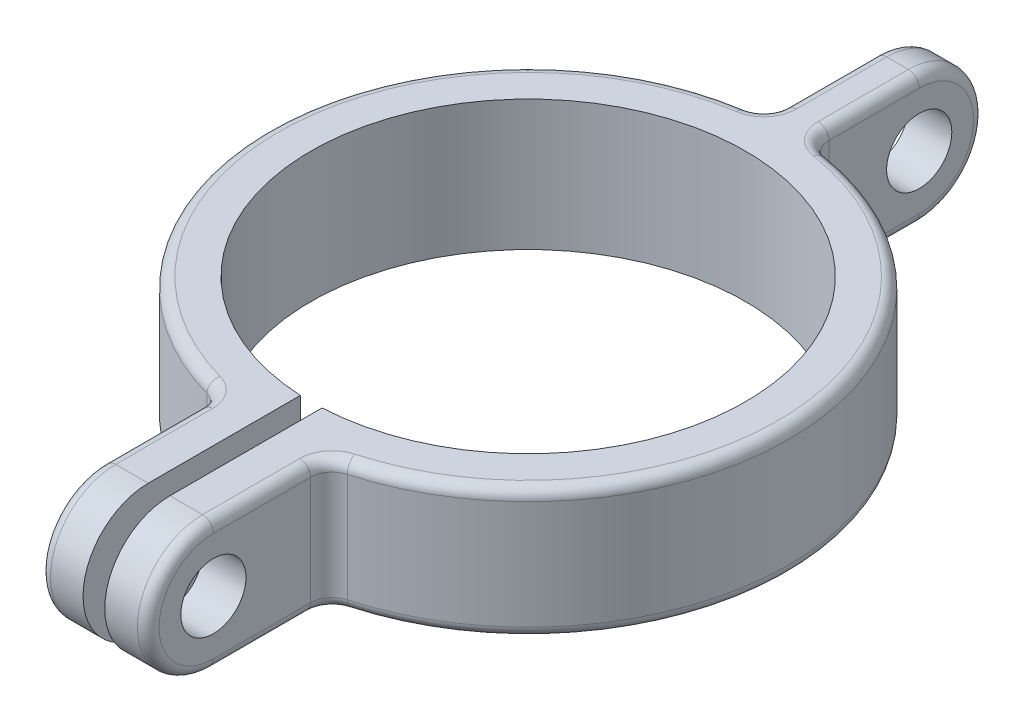
SolidWorks part; units mm, degrees
ref_plane "Front" through (0, 0, 0) normal (0, 0, 1) x (1, 0, 0)
ref_plane "Top" through (0, 0, 0) normal (0, 1, 0) x (1, 0, 0)
ref_plane "Right" through (0, 0, 0) normal (1, 0, 0) x (0, 0, -1)
sketch "Sketch1" plane through (0, 0, 0) normal (0, 1, 0) x (1, 0, 0)
  circle A0 centre (0, 0) radius 38.1
  circle A1 centre (0, 0) radius 31.75
  dimension "D1" = 63.5
  dimension "D2" = 76.2
extrude "Extrude1" add sketch "Sketch1" along normal blind 19.05
sketch "Sketch2" plane through (0, 19.05, 0) normal (0, 1, 0) x (-1, 0, 0)
  line L1 (-1.5875, 0) -> (1.5875, 0)
  line L2 (-1.5875, 0) -> (-1.5875, 40.64)
  line L3 (-1.5875, 40.64) -> (1.5875, 40.64)
  line L4 (1.5875, 0) -> (1.5875, 40.64)
  circle A0 centre (0, 0) radius 38.1 construction
  dimension "D2" = 2.54
  dimension "D1" = 3.175
extrude "Cut-Extrude1" cut sketch "Sketch2" against normal through all
sketch "Sketch3" plane through (1.5875, 0, 0) normal (-1, 0, 0) x (0, 0, 1)
  line L0 (31.7103, 19.05) -> (53.9419, 19.05)
  line L1 (53.9419, 0) -> (31.7103, 0)
  line L2 (31.7103, 19.05) -> (31.7103, 0)
  line L3 (38.0669, 0) -> (38.0669, 19.05) construction
  arc A0 (53.9419, 19.05) -> (53.9419, 0) centre (53.9419, 9.525) cw
  dimension "D1" = 15.875
extrude "Extrude2" add sketch "Sketch3" against normal blind 6.35
mirror "Mirror1" about plane through (0, 0, 0) normal (1, 0, 0) of "Extrude2"
sketch "Sketch6" plane through (7.9375, 0, 0) normal (1, 0, 0) x (0, 0, -1)
  circle A0 centre (-53.9419, 9.525) radius 4.7625
  dimension "D1" = 9.525
extrude "Cut-Extrude3" cut sketch "Sketch6" against normal through all
sketch "Sketch7" plane through (0, 0, 0) normal (1, 0, 0) x (0, 0, -1)
  line L0 (31.75, 19.05) -> (53.975, 19.05)
  line L2 (53.975, 0) -> (31.75, 0)
  line L4 (31.75, 0) -> (31.75, 19.05)
  line L9 (38.1, 0) -> (38.1, 19.05) construction
  arc A0 (53.975, 19.05) -> (53.975, 0) centre (53.975, 9.525) cw
  dimension "D1" = 15.875
extrude "Extrude4" add sketch "Sketch7" along normal mid plane 6.35
fillet "Fillet4" radius 3.175 4 edges at (-7.9375, 9.525, 37.264) (7.9375, 9.525, 37.264) (3.175, 9.525, -37.9675) (-3.175, 9.525, -37.9675)
sketch "Sketch10" plane through (3.175, 0, 0) normal (1, 0, 0) x (0, 0, -1)
  circle A0 centre (53.975, 9.525) radius 4.7625
  dimension "D1" = 9.525
extrude "Cut-Extrude6" cut sketch "Sketch10" against normal through all
fillet "Fillet5" radius 1.5875 24 edges at (-3.175, 9.525, -63.5) (-3.175, 0, -47.3793) (-3.9384, 19.05, -38.7185) (-3.9384, 0, -38.7185) (-38.0336, 0, -2.2492) (-38.0336, 19.05, -2.2492) (-8.5832, 0, 37.8318) (-8.5832, 19.05, 37.8318) (-7.9375, 19.05, 46.8464) (-7.9375, 0, 46.8464) (-7.9375, 9.525, 63.4669) (3.175, 9.525, -63.5) (3.175, 0, -47.3793) (3.9384, 19.05, -38.7185) (3.9384, 0, -38.7185) (38.0336, 19.05, -2.2492) (38.0336, 0, -2.2492) (8.5832, 19.05, 37.8318) (8.5832, 0, 37.8318) (7.9375, 0, 46.8464) (7.9375, 9.525, 63.4669) (7.9375, 19.05, 46.8464) (-3.175, 19.05, -47.3793) (3.175, 19.05, -47.3793)
